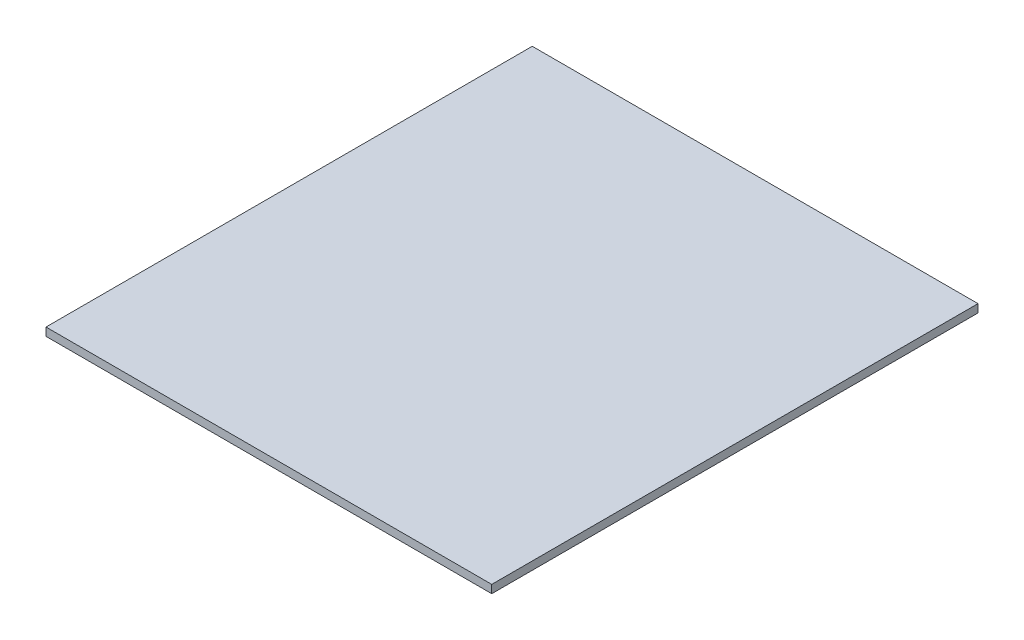
SolidWorks part; units mm, degrees
ref_plane "前视基准面" through (0, 0, 0) normal (0, 0, 1) x (1, 0, 0)
ref_plane "上视基准面" through (0, 0, 0) normal (0, 1, 0) x (1, 0, 0)
ref_plane "右视基准面" through (0, 0, 0) normal (1, 0, 0) x (0, 0, -1)
sketch "草图1" plane through (0, 0, 0) normal (0, 1, 0) x (1, 0, 0)
  line L1 (-55, 60) -> (55, 60)
  line L2 (-55, 60) -> (-55, -60)
  line L3 (-55, -60) -> (55, -60)
  line L4 (55, 60) -> (55, -60)
  line L5 (-55, 60) -> (55, -60) construction
  line L6 (-55, -60) -> (55, 60) construction
  point P0 (0, 0)
  dimension "D1" = 120
  dimension "D2" = 110
extrude "凸台-拉伸1" add sketch "草图1" along normal blind 2
